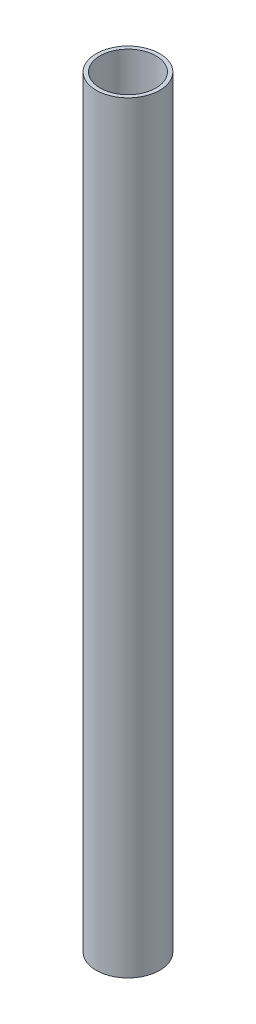
SolidWorks part; units mm, degrees
ref_plane "Front Plane" through (0, 0, 0) normal (0, 0, 1) x (1, 0, 0)
ref_plane "Top Plane" through (0, 0, 0) normal (0, 1, 0) x (1, 0, 0)
ref_plane "Right Plane" through (0, 0, 0) normal (1, 0, 0) x (0, 0, -1)
sketch "Sketch1" plane through (0, 0, 0) normal (0, 1, 0) x (1, 0, 0)
  circle A0 centre (0, 0) radius 12.7
  circle A1 centre (0, 0) radius 11.176
  dimension "D1" = 25.4
  dimension "D2" = 22.352
extrude "Boss-Extrude1" add sketch "Sketch1" along normal blind 304.8
